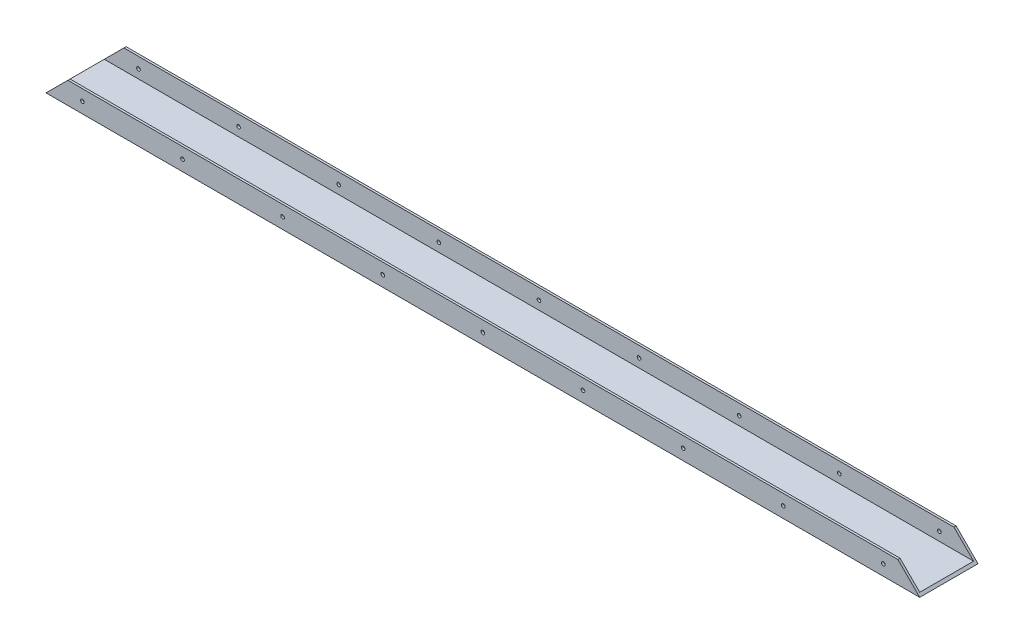
SolidWorks part; units mm, degrees
ref_plane "Alzado" through (0, 0, 0) normal (0, 0, 1) x (1, 0, 0)
ref_plane "Planta" through (0, 0, 0) normal (0, 1, 0) x (1, 0, 0)
ref_plane "Vista lateral" through (0, 0, 0) normal (1, 0, 0) x (0, 0, -1)
sketch "Croquis1" plane through (0, 0, 0) normal (1, 0, 0) x (0, 0, -1)
  line L0 (-20, 0) -> (20, 0)
  line L1 (20, 0) -> (20, 15)
  line L2 (20, 15) -> (18.5, 15)
  line L3 (18.5, 15) -> (18.5, 1.5)
  line L4 (18.5, 1.5) -> (-18.5, 1.5)
  line L5 (-18.5, 1.5) -> (-18.5, 15)
  line L6 (-18.5, 15) -> (-20, 15)
  line L7 (-20, 15) -> (-20, 0)
  point P4 (0, 0)
extrude "Saliente-Extruir1" add sketch "Croquis1" along normal blind 600
sketch "Croquis2" plane through (0, 0, -20) normal (0, 0, -1) x (-1, 0, 0)
  line L0 (-600, 15) -> (-585, 15)
  line L1 (-585, 15) -> (-600, 0)
  line L2 (-600, 0) -> (-600, 15)
  line L3 (0, 15) -> (-15, 15)
  line L4 (-600, 15) -> (0, 15) construction
  line L5 (-15, 15) -> (0, 0)
  line L6 (0, 0) -> (0, 15)
  line L7 (0, 0) -> (-600, 0) construction
  line L8 (-7.5, 7.5) -> (-592.5, 7.5) construction
  line L9 (-7.5, 7.5) -> (-25, 7.5) construction
  line L10 (-25, 7.5) -> (-300, 7.5) construction
  line L11 (-300, 7.5) -> (-162.5, 7.5) construction
  line L12 (-162.5, 7.5) -> (-25, 7.5) construction
  line L13 (-25, 7.5) -> (-93.75, 7.5) construction
  line L14 (-93.75, 7.5) -> (-300, 7.5) construction
  line L15 (-300, 7.5) -> (-162.5, 7.5) construction
  line L16 (-162.5, 7.5) -> (-231.25, 7.5) construction
  line L17 (-437.5, 7.5) -> (-368.75, 7.5) construction
  line L18 (-575, 7.5) -> (-506.25, 7.5) construction
  line L19 (-437.5, 7.5) -> (-575, 7.5) construction
  circle A0 centre (-25, 7.5) radius 1.25
  circle A1 centre (-93.75, 7.5) radius 1.25
  circle A2 centre (-162.5, 7.5) radius 1.25
  circle A3 centre (-231.25, 7.5) radius 1.25
  circle A4 centre (-368.75, 7.5) radius 1.25
  circle A5 centre (-437.5, 7.5) radius 1.25
  circle A6 centre (-506.25, 7.5) radius 1.25
  circle A7 centre (-575, 7.5) radius 1.25
  circle A8 centre (-300, 7.5) radius 1.25
extrude "Cortar-Extruir1" cut sketch "Croquis2" against normal through all
